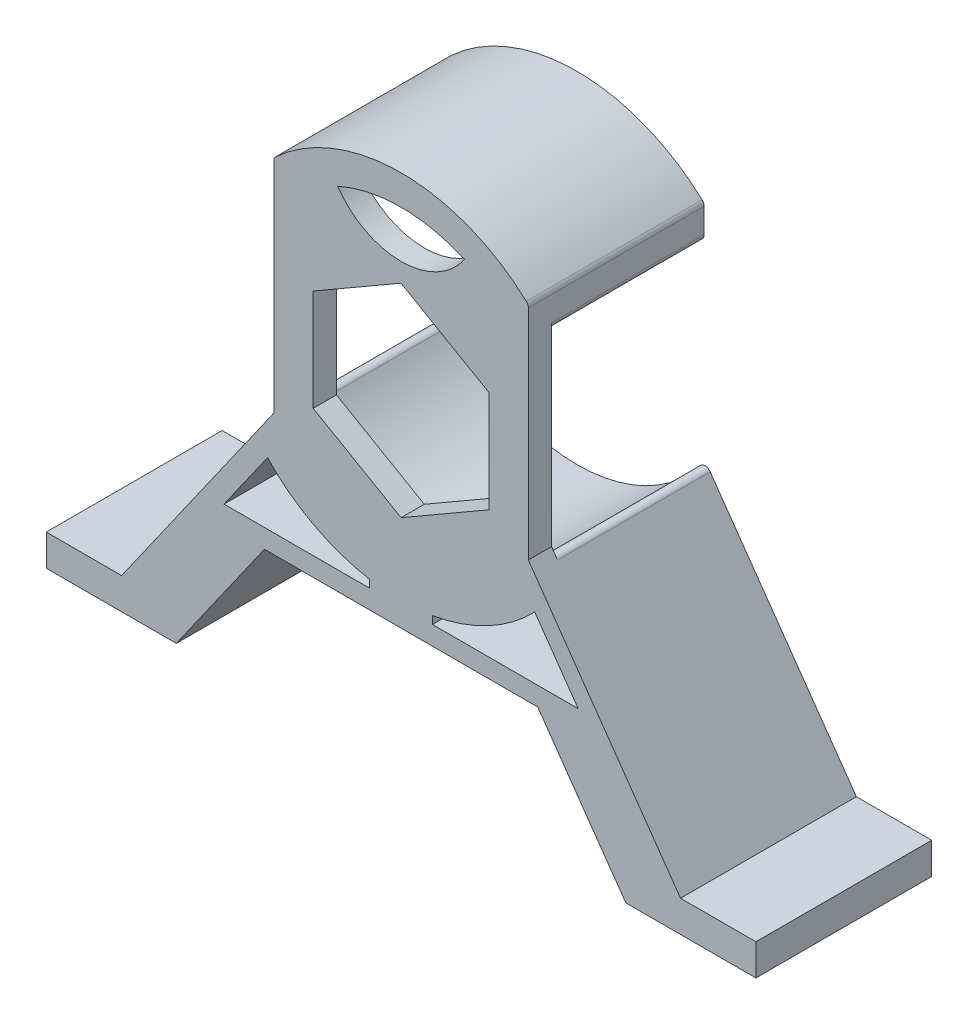
SolidWorks part; units mm, degrees
ref_plane "Plan de face" through (0, 0, 0) normal (0, 0, 1) x (1, 0, 0)
ref_plane "Plan de dessus" through (0, 0, 0) normal (0, 1, 0) x (1, 0, 0)
ref_plane "Plan de droite" through (0, 0, 0) normal (1, 0, 0) x (0, 0, -1)
sketch "Esquisse1" plane through (0, 0, 0) normal (0, 0, 1) x (1, 0, 0)
  line L0 (0, -82.8168) -> (0, -62.5845) construction
  line L1 (-56.5, 0) -> (-56.5, 5)
  line L2 (-56.5, 5) -> (-44.5, 5)
  line L3 (-44.5, -84.7669) -> (-44.5, -25.7476) construction
  line L4 (-56.5, 0) -> (-35.792, 0)
  line L6 (-35.792, 0) -> (-21.7522, 20)
  line L12 (-21.7522, 20) -> (21.7522, 20)
  line L13 (-44.5, 5) -> (-20.2622, 39.5272)
  line L14 (22.5, 62.9954) -> (-22.5, 62.9954) construction
  line L22 (35.792, 0) -> (21.7522, 20)
  line L24 (56.5, 5) -> (44.5, 5)
  line L25 (56.5, 0) -> (56.5, 5)
  line L26 (56.5, 0) -> (35.792, 0)
  line L28 (-20.2622, 39.5272) -> (-20.2622, 74.7404)
  line L30 (20.2622, 39.5272) -> (20.2622, 74.7404)
  line L31 (44.5, 5) -> (20.2622, 39.5272)
  line L32 (-18.291, 37) -> (0, 37) construction
  line L33 (0, 28.55) -> (-27.9681, 28.55) construction
  circle A1 centre (0, 53.3) radius 24.5 construction
  arc A2 (-20.2622, 39.0872) -> (0, 28.55) centre (0, 53.3) ccw construction
  arc A3 (20.2622, 74.7404) -> (-20.2622, 74.7404) centre (0, 53.3) ccw
  circle A4 centre (0, 40.5) radius 3.5 construction
  point P32 (0, 20)
  dimension "D1" = 20
  dimension "D7" = 49
  dimension "D11" = 8.45
  dimension "D8" = 0.25
  dimension "D9" = 5
  dimension "D13" = 7
  dimension "D2" = 5
  dimension "D3" = 12
  dimension "D4" = 21.7522
  dimension "D5" = 125.069
  dimension "D6" = 56.5
  dimension "D10" = 45
  dimension "D12" = 40.5
extrude "Boss.-Extru.1" add sketch "Esquisse1" along normal blind 28
sketch "Esquisse2" plane through (0, 0, 0) normal (0, 0, 1) x (1, 0, 0)
  circle A0 centre (0, 53.3) radius 24.75
  arc A1 (20.2622, 74.7404) -> (-20.2622, 74.7404) centre (0, 53.3) ccw construction
  circle A3 centre (0, 53.3) radius 24.5 construction
  dimension "D1" = 0.25
extrude "Enlèv. mat.-Extru.1" cut sketch "Esquisse2" along normal blind 24.3
sketch "Esquisse5" plane through (0, 0, 28) normal (0, 0, 1) x (1, 0, 0)
  line L0 (0, 67.5658) -> (0, 82.8) construction
  line L1 (0, 67.5658) -> (-14, 59.4829)
  line L2 (-14, 59.4829) -> (-14, 43.3171)
  line L3 (-14, 43.3171) -> (0, 35.2342)
  line L4 (0, 35.2342) -> (14, 43.3171)
  line L5 (14, 43.3171) -> (14, 59.4829)
  line L6 (14, 59.4829) -> (0, 67.5658)
  line L7 (0, 35.2342) -> (0, 20) construction
  line L8 (-21.7522, 20) -> (21.7522, 20) construction
  line L12 (-21.2746, 32.8637) -> (-28.1988, 23)
  line L14 (0, 70.5658) -> (-20.2622, 70.5658) construction
  line L18 (-28.1988, 23) -> (-5, 23)
  line L19 (-5, 23) -> (-5, 24.2268)
  line L24 (-20.2622, 74.7404) -> (-20.2622, 39.5272) construction
  line L25 (-20.2622, 39.5272) -> (-44.5, 5) construction
  line L26 (21.2746, 32.8637) -> (28.1988, 23)
  line L27 (28.1988, 23) -> (5, 23)
  line L28 (5, 23) -> (5, 24.2268)
  circle A0 centre (0, 51.4) radius 14 construction
  arc A2 (20.2622, 74.7404) -> (-20.2622, 74.7404) centre (0, 53.3) ccw construction
  arc A6 (-10.0997, 75.8955) -> (10.0997, 75.8955) centre (0, 82.8) ccw
  arc A7 (20.2622, 67.5128) -> (-20.2622, 67.5128) centre (0, 53.3) ccw construction
  arc A8 (-10.0997, 75.8955) -> (10.0997, 75.8955) centre (0, 53.3) cw
  circle A9 centre (0, 53.3) radius 29.5 construction
  arc A10 (20.2622, 74.7404) -> (-20.2622, 74.7404) centre (0, 53.3) ccw construction
  arc A11 (-5, 24.2268) -> (-21.2746, 32.8637) centre (0, 53.3) cw
  arc A12 (5, 24.2268) -> (21.2746, 32.8637) centre (0, 53.3) ccw
  dimension "D1" = 28
  dimension "D4" = 5
  dimension "D2" = 3
  dimension "D3" = 3
  dimension "D5" = 3
extrude "Enlèv. mat.-Extru.6" cut sketch "Esquisse5" against normal through all
fillet "Congé1" radius 1 6 edges at (-20.4157, 39.3085, 12.15) (20.4157, 39.3085, 12.15) (-20.2622, 74.7404, 14) (20.2622, 74.7404, 14) (-20.2622, 67.5128, 12.15) (20.2622, 67.5128, 12.15)
